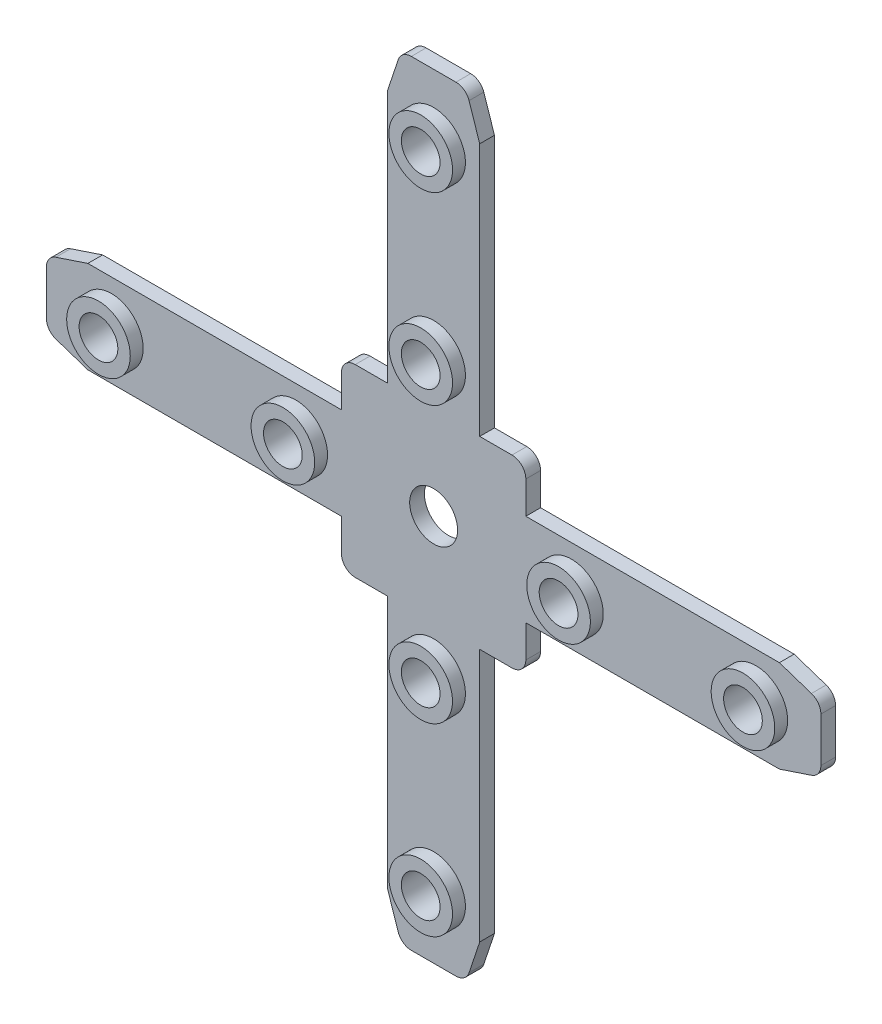
SolidWorks part; units mm, degrees
material "Plain Carbon Steel"
ref_plane "Front Plane" through (0, 0, 0) normal (0, 0, 1) x (1, 0, 0)
ref_plane "Top Plane" through (0, 0, 0) normal (0, 1, 0) x (1, 0, 0)
ref_plane "Right Plane" through (0, 0, 0) normal (1, 0, 0) x (0, 0, -1)
sketch "Sketch1" plane through (0, 0, 0) normal (0, 0, 1) x (1, 0, 0)
  line L0 (-10, 0) -> (0, 0) construction
  line L1 (0, 0) -> (0, 41.985) construction
  line L2 (-10, -8.5) -> (-10, -5)
  line L3 (-8.5, 10) -> (-5, 10)
  line L4 (-5, 10) -> (-5, 37.485)
  line L5 (-5, 37.485) -> (-3.8419, 40.9593)
  line L6 (-2.4189, 41.985) -> (2.4189, 41.985)
  line L7 (5, 37.485) -> (3.8419, 40.9593)
  line L8 (5, 10) -> (5, 37.485)
  line L9 (8.5, 10) -> (5, 10)
  line L10 (10, -8.5) -> (10, -5)
  line L11 (8.5, -10) -> (5, -10)
  line L12 (5, -10) -> (5, -37.485)
  line L13 (5, -37.485) -> (3.8419, -40.9593)
  line L14 (-2.4189, -41.985) -> (2.4189, -41.985)
  line L15 (-5, -37.485) -> (-3.8419, -40.9593)
  line L16 (-5, -10) -> (-5, -37.485)
  line L17 (-8.5, -10) -> (-5, -10)
  line L18 (-10, 5) -> (-37.5, 5)
  line L19 (-37.5, 5) -> (-40.9743, 3.8419)
  line L20 (-42, 2.4189) -> (-42, -2.4189)
  line L21 (-37.5, -5) -> (-40.9743, -3.8419)
  line L22 (-10, -5) -> (-37.5, -5)
  line L23 (-10, 5) -> (-10, 8.5)
  line L24 (10, -5) -> (37.5, -5)
  line L25 (37.5, -5) -> (40.9743, -3.8419)
  line L26 (42, 2.4189) -> (42, -2.4189)
  line L27 (37.5, 5) -> (40.9743, 3.8419)
  line L28 (10, 5) -> (37.5, 5)
  line L29 (10, 5) -> (10, 8.5)
  circle A0 centre (0, 0) radius 2.6
  arc A1 (-2.4189, -41.985) -> (-3.8419, -40.9593) centre (-2.4189, -40.485) cw
  arc A2 (3.8419, -40.9593) -> (2.4189, -41.985) centre (2.4189, -40.485) cw
  arc A3 (-3.8419, 40.9593) -> (-2.4189, 41.985) centre (-2.4189, 40.485) cw
  arc A4 (3.8419, 40.9593) -> (2.4189, 41.985) centre (2.4189, 40.485) ccw
  arc A5 (-8.5, -10) -> (-10, -8.5) centre (-8.5, -8.5) cw
  arc A6 (-10, 8.5) -> (-8.5, 10) centre (-8.5, 8.5) cw
  arc A7 (8.5, 10) -> (10, 8.5) centre (8.5, 8.5) cw
  arc A8 (8.5, -10) -> (10, -8.5) centre (8.5, -8.5) ccw
  arc A9 (-40.9743, -3.8419) -> (-42, -2.4189) centre (-40.5, -2.4189) cw
  arc A10 (-40.9743, 3.8419) -> (-42, 2.4189) centre (-40.5, 2.4189) ccw
  arc A11 (40.9743, 3.8419) -> (42, 2.4189) centre (40.5, 2.4189) cw
  arc A12 (40.9743, -3.8419) -> (42, -2.4189) centre (40.5, -2.4189) ccw
  point P24 (-3.5, -41.985)
  point P27 (3.5, -41.985)
  point P30 (-3.5, 41.985)
  point P33 (3.5, 41.985)
  point P36 (-10, -10)
  point P39 (-10, 10)
  point P42 (10, 10)
  point P45 (10, -10)
  point P51 (-42, 0)
  point P55 (-42, -3.5)
  point P58 (-42, 3.5)
  point P65 (42, 0)
  dimension "D4" = 5.2
  dimension "D8" = 1.5
  dimension "D9" = 10
  dimension "D10" = 32
  dimension "D11" = 4.5
  dimension "D13" = 1.5
  dimension "D1" = 20
  dimension "D2" = 20
  dimension "D3" = 10
  dimension "D5" = 4.5
  dimension "D6" = 83.97
  dimension "D7" = 7
  dimension "D12" = 7
extrude "Boss-Extrude1" add sketch "Sketch1" along normal blind 1.6
sketch "Sketch2" plane through (0, 0, 1.6) normal (0, 0, 1) x (1, 0, 0)
  line L0 (-42, 0) -> (0, 0) construction
  line L2 (0, 0) -> (0, 41.985) construction
  line L3 (2.4189, 41.985) -> (-2.4189, 41.985) construction
  line L4 (-42, 2.4189) -> (-42, -2.4189) construction
  circle A0 centre (0, 14.95) radius 3.45
  circle A1 centre (0, 34.95) radius 3.45
  circle A2 centre (0, -14.95) radius 3.45
  circle A3 centre (0, -34.95) radius 3.45
  circle A4 centre (-14.95, 0) radius 3.45
  circle A5 centre (-34.95, 0) radius 3.45
  circle A6 centre (0, 0) radius 2.6 construction
  circle A7 centre (14.95, 0) radius 3.45
  circle A8 centre (34.95, 0) radius 3.45
  dimension "D1" = 6.9
  dimension "D3" = 14.95
  dimension "D5" = 14.95
  dimension "D2" = 20
  dimension "D4" = 20
extrude "Boss-Extrude2" add sketch "Sketch2" along normal blind 1.4
hole_wizard "M5x0.8 Tapped Hole1" positions "Sketch4" profile "Sketch3" tap size "M5x0.8" standard "ANSI Metric" end condition through all
sketch "Sketch4" plane through (0, 0, 3) normal (0, 0, 1) x (1, 0, 0)
  point P0 (0, 34.95)
  point P3 (0, 14.95)
  point P6 (0, -14.95)
  point P9 (0, -34.95)
  point P13 (-14.95, 0)
  point P16 (-34.95, 0)
  point P20 (14.95, 0)
  point P23 (34.95, 0)
sketch "Sketch3" plane through (0, 34.95, 3) normal (1, 0, 0) x (0, -1, 0)
  line L0 (0, 0) -> (0, 3)
  line L1 (0, 3) -> (2.1, 3)
  line L2 (2.1, 3) -> (2.1, 0)
  line L5 (2.1, 0) -> (0, 0)
  line L11 (0, -6.35) -> (0, 107.95) construction
  dimension "Thru Tap Drill Dia." = 4.2
  dimension "Thru Tap Drill Depth" = 3
cosmetic thread "Hole Thread1" parameters "D2"=5
cosmetic thread "Hole Thread2" parameters "D2"=5
cosmetic thread "Hole Thread3" parameters "D2"=5
cosmetic thread "Hole Thread4" parameters "D2"=5
cosmetic thread "Hole Thread5" parameters "D2"=5
cosmetic thread "Hole Thread6" parameters "D2"=5
cosmetic thread "Hole Thread7" parameters "D2"=5
cosmetic thread "Hole Thread8" parameters "D2"=5
